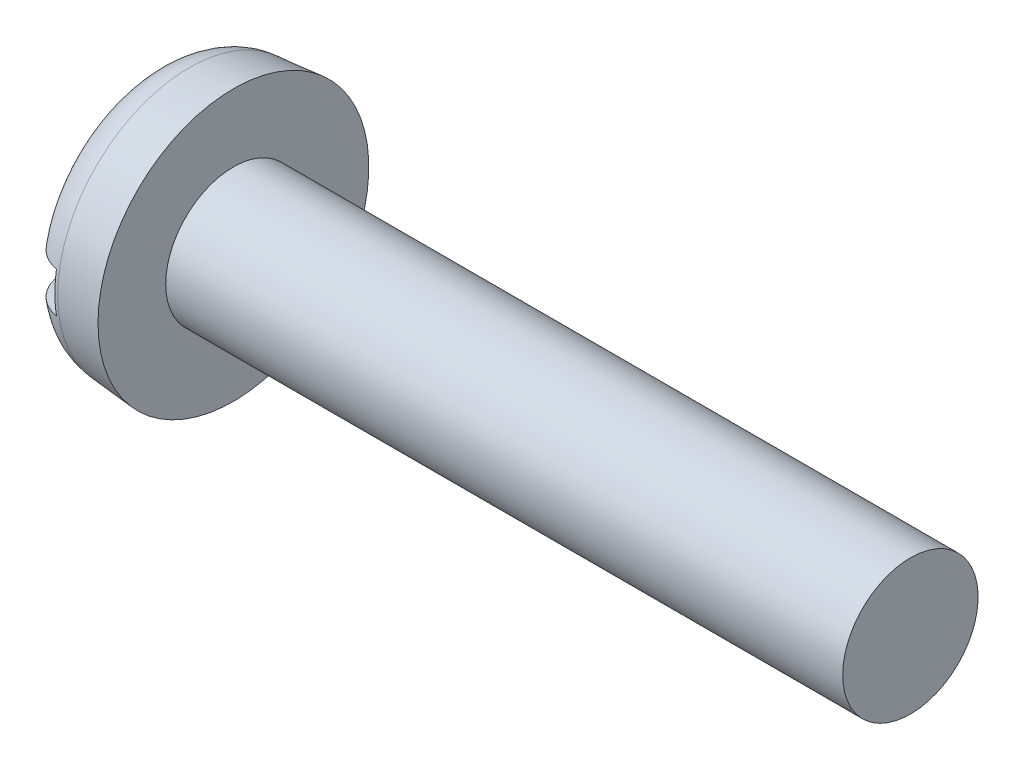
SolidWorks part; units mm, degrees
ref_plane "Plane1" through (0, 0, 0) normal (0, 0, 1) x (1, 0, 0)
ref_plane "Plane2" through (0, 0, 0) normal (0, 1, 0) x (1, 0, 0)
ref_plane "Plane3" through (0, 0, 0) normal (1, 0, 0) x (0, 0, -1)
sketch "BodySke" plane through (0, 0, 0) normal (0, 0, 1) x (1, 0, 0)
  line L0 (2.4, 2) -> (2.4, 4)
  line L1 (0, 0) -> (0, 3.79)
  line L2 (-25.4, 0) -> (127, 0) construction
  line L3 (22.4, 0) -> (0, 0)
  line L4 (2.4, 2) -> (22.4, 2)
  line L5 (22.4, 2) -> (22.4, 0)
  line L6 (0, 3.79) -> (2.4, 4)
  line L9 (3.1, 3.5875) -> (3.1, -5.9375) construction
  line L10 (2.4, 6.35) -> (2.4, -3.175) construction
  dimension "Length" = 20
  dimension "Head_ht" = 2.4
  dimension "Advance" = 0.7
  dimension "Thread_nom" = 20
  dimension "Head_dia" = 8
  dimension "Head_side_angle" = 5
  dimension "Diameter" = 4
revolve "Base-Revolve" add sketch "BodySke"
cosmetic thread "ThreadCosmetic" [suppressed]
fillet "Fillet1" [suppressed] radius 0.2
fillet "Fillet2" radius 1.2 1 edges at (0, 0, 3.79)
sketch "Sketch2" plane through (0, 0, 0) normal (1, 0, 0) x (0, 0, -1)
  line L0 (4, -0.6) -> (-4, -0.6)
  line L1 (4, -0.6) -> (4, 0.6)
  line L2 (-4, 0.6) -> (4, 0.6)
  line L3 (-4, 0.6) -> (-4, -0.6)
  dimension "D1" = 8
  dimension "Slot_width" = 1.2
  dimension "D2" = 4
  dimension "D3" = 0.6
extrude "Slot" cut sketch "Sketch2" along normal blind 1
sketch "ThdSchSke" plane through (0, 0, 0) normal (0, 0, 1) x (1, 0, 0)
  line L0 (3.8, -1.61) -> (3.5269, -2)
  line L1 (3.8, -1.61) -> (4.0731, -2)
  line L2 (4.0731, -2) -> (4.0731, -2.5)
  line L3 (-3.175, 0) -> (5.1513, 0) construction
  line L5 (4.0731, -2.5) -> (3.5269, -2.5)
  line L6 (3.5269, -2.5) -> (3.5269, -2)
  dimension "Diameter" = 4
  dimension "SideAngle" = 55
  dimension "VeeAngle" = 70
  dimension "Thread_minor" = 3.22
  dimension "Overcut" = 5
  dimension "Start" = 3.8
revolve "ThreadSchematic" [suppressed] cut sketch "ThdSchSke" angle 360 about L3
pattern_linear "ThdSchPat" [suppressed]
equation "\"D1@Sketch2\" = \"Head_dia@BodySke\""
equation "\"D2@Sketch2\" = \"D1@Sketch2\" / 2"
equation "\"D3@Sketch2\" = \"Slot_width@Sketch2\" / 2"
equation "\"Thread_length@ThreadCosmetic\" = ((sgn( (\"Length@BodySke\" - \"Advance@BodySke\" * 2.0 ) - \"Thread_nom@BodySke\" )-1)*( (\"Length@BodySke\" - \"Advance@BodySke\"  * 2.0) - \"Thread_nom@BodySke\" ))/-2+ \"Thread_nom@BodySke\""
equation "\"Thread_minor@ThdSchSke\" = \"Thread_minor@ThreadCosmetic\""
equation "\"Diameter@ThdSchSke\" = \"Diameter@BodySke\""
equation "\"Overcut@ThdSchSke\" = \"Diameter@BodySke\" * 1.25"
equation "\"Start@ThdSchSke\" = \"Head_ht@BodySke\" + \"Length@BodySke\" - \"Thread_length@ThreadCosmetic\"  '---Non-countersunk---"
equation "\"Num_threads@ThdSchPat\" = int( \"Thread_length@ThreadCosmetic\" / \"Advance@BodySke\" + 0.999 )  + 1"
equation "\"Advance@ThdSchPat\" = \"Thread_length@ThreadCosmetic\" /  (\"Num_threads@ThdSchPat\" - 1) 'relax it"
